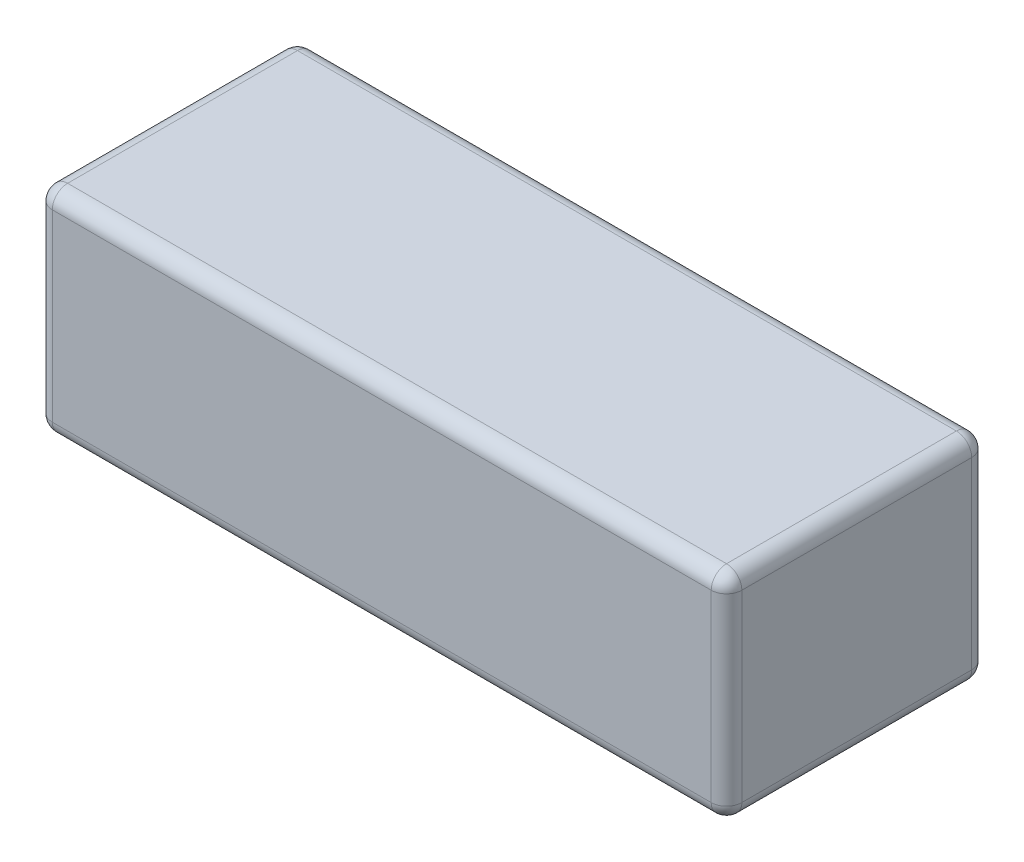
SolidWorks part; units mm, degrees
ref_plane "Front Plane" through (0, 0, 0) normal (0, 0, 1) x (1, 0, 0)
ref_plane "Top Plane" through (0, 0, 0) normal (0, 1, 0) x (1, 0, 0)
ref_plane "Right Plane" through (0, 0, 0) normal (1, 0, 0) x (0, 0, -1)
sketch "Sketch1" plane through (0, 0, 0) normal (0, 1, 0) x (1, 0, 0)
  line L1 (-45, 17) -> (45, 17)
  line L2 (-45, 17) -> (-45, -17)
  line L3 (-45, -17) -> (45, -17)
  line L4 (45, 17) -> (45, -17)
  line L5 (-45, 17) -> (45, -17) construction
  line L6 (-45, -17) -> (45, 17) construction
  point P0 (0, 0)
  dimension "D1" = 34
  dimension "D2" = 90
extrude "Boss-Extrude1" add sketch "Sketch1" along normal blind 28
fillet "Fillet1" radius 2 12 edges at (45, 14, 17) (0, 0, 17) (45, 0, 0) (-45, 14, 17) (-45, 0, 0) (0, 28, 17) (-45, 28, 0) (45, 28, 0) (45, 14, -17) (0, 28, -17) (-45, 14, -17) (0, 0, -17)
